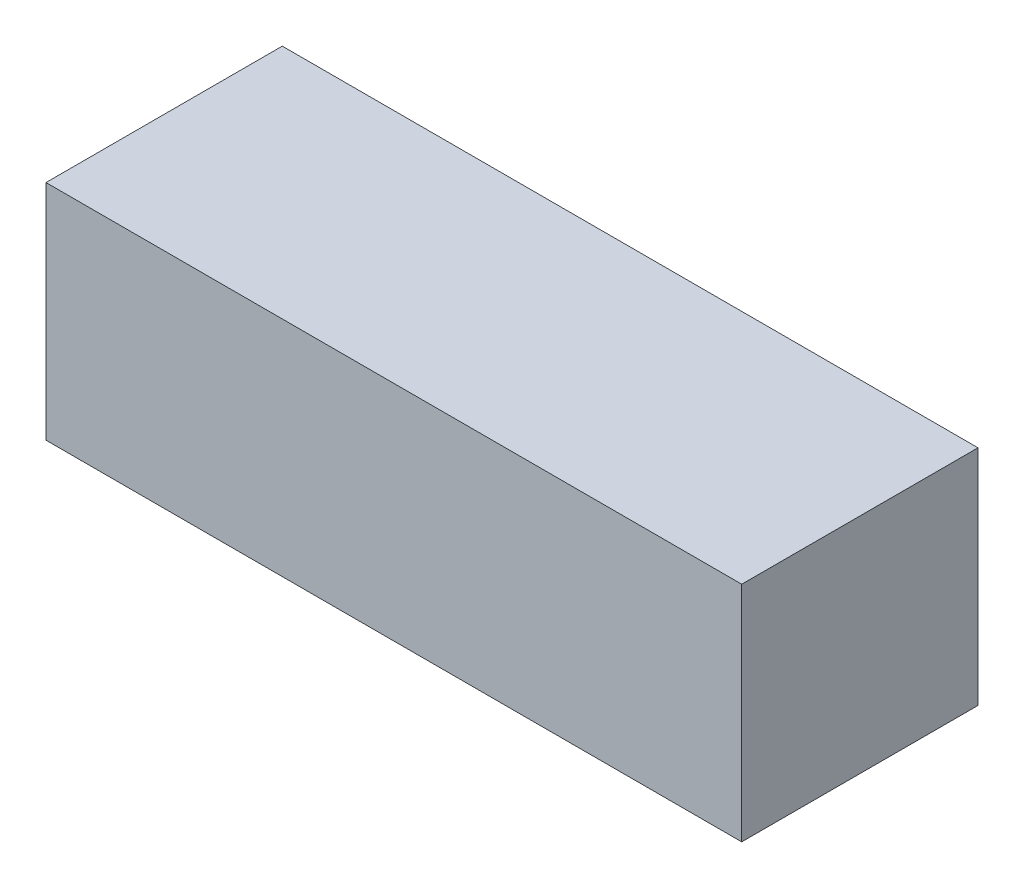
SolidWorks part; units mm, degrees
ref_plane "Front Plane" through (0, 0, 0) normal (0, 0, 1) x (1, 0, 0)
ref_plane "Top Plane" through (0, 0, 0) normal (0, 1, 0) x (1, 0, 0)
ref_plane "Right Plane" through (0, 0, 0) normal (1, 0, 0) x (0, 0, -1)
sketch "Sketch1" plane through (0, 0, 0) normal (1, 0, 0) x (0, 0, -1)
  line L1 (-9, 8.5) -> (9, 8.5)
  line L2 (-9, 8.5) -> (-9, -8.5)
  line L3 (-9, -8.5) -> (9, -8.5)
  line L4 (9, 8.5) -> (9, -8.5)
  line L5 (-9, 8.5) -> (9, -8.5) construction
  line L6 (-9, -8.5) -> (9, 8.5) construction
  point P0 (0, 0)
  dimension "D1" = 18
  dimension "D2" = 17
extrude "Boss-Extrude1" add sketch "Sketch1" along normal blind 53
